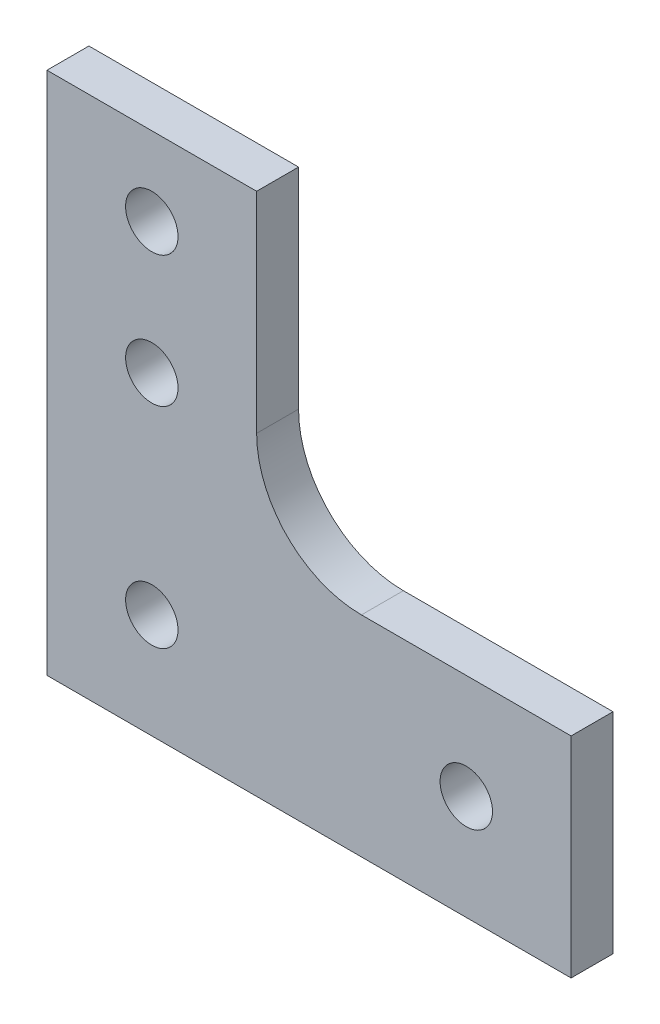
SolidWorks part; units mm, degrees
ref_plane "Front Plane" through (0, 0, 0) normal (0, 0, 1) x (1, 0, 0)
ref_plane "Top Plane" through (0, 0, 0) normal (0, 1, 0) x (1, 0, 0)
ref_plane "Right Plane" through (0, 0, 0) normal (1, 0, 0) x (0, 0, -1)
sketch "Sketch1" plane through (0, 0, 0) normal (0, 0, 1) x (1, 0, 0)
  line L0 (-20, -10) -> (-20, 40)
  line L3 (-20, 40) -> (0, 40)
  line L4 (30, -10) -> (30, 10)
  line L5 (30, 10) -> (10, 10)
  line L8 (0, 40) -> (0, 20)
  line L9 (30, -10) -> (-20, -10)
  line L10 (0, 20) -> (0, 10)
  line L11 (0, 10) -> (10, 10)
  circle A0 centre (-10, 32.5) radius 2.5
  circle A1 centre (-10, 0) radius 2.5
  circle A3 centre (20, 0) radius 2.5
  circle A7 centre (-10, 20) radius 2.5
  dimension "D5" = 20
  dimension "D6" = 10
  dimension "D7" = 20
  dimension "D8" = 5
  dimension "D9" = 5
  dimension "D12" = 10
  dimension "D13" = 10
  dimension "D18" = 5
  dimension "D19" = 7.5
  dimension "D20" = 5
  dimension "D21" = 12.5
  dimension "D10" = 10
  dimension "D11" = 10
  dimension "D28" = 10
  dimension "D29" = 10
  dimension "D22" = 30
  dimension "D32" = 20
  dimension "D34" = 30
extrude "Boss-Extrude1" add sketch "Sketch1" along normal blind 4
fillet "Fillet1" radius 10 1 edges at (0, 10, 2)
